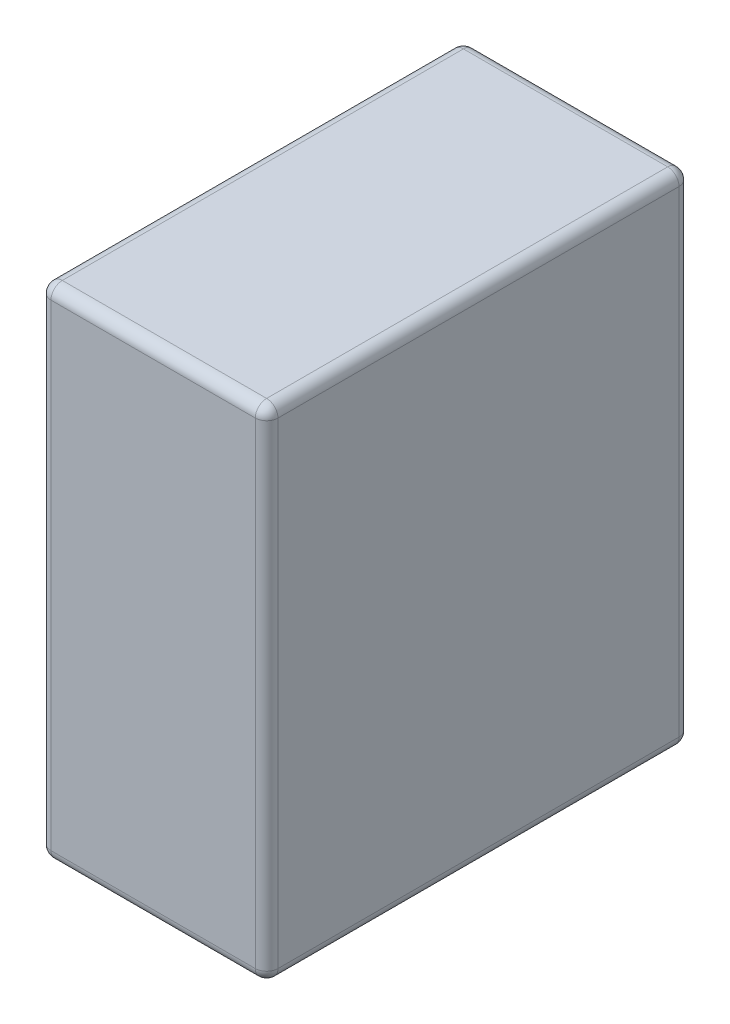
SolidWorks part; units mm, degrees
ref_plane "Alzado" through (0, 0, 0) normal (0, 0, 1) x (1, 0, 0)
ref_plane "Planta" through (0, 0, 0) normal (0, 1, 0) x (1, 0, 0)
ref_plane "Vista lateral" through (0, 0, 0) normal (1, 0, 0) x (0, 0, -1)
sketch "Croquis1" plane through (0, 0, 0) normal (0, 1, 0) x (1, 0, 0)
  line L1 (15, -28) -> (-15, -28)
  line L2 (15, -28) -> (15, 28)
  line L3 (15, 28) -> (-15, 28)
  line L4 (-15, -28) -> (-15, 28)
  line L5 (15, -28) -> (-15, 28) construction
  line L6 (15, 28) -> (-15, -28) construction
  point P0 (0, 0)
  dimension "D1" = 56
  dimension "D2" = 30
extrude "Saliente-Extruir1" add sketch "Croquis1" along normal blind 66
fillet "Redondeo1" radius 1.5 12 edges at (-15, 0, 0) (-15, 33, -28) (0, 0, -28) (15, 33, -28) (15, 0, 0) (-15, 33, 28) (15, 33, 28) (0, 0, 28) (0, 66, -28) (15, 66, 0) (0, 66, 28) (-15, 66, 0)
